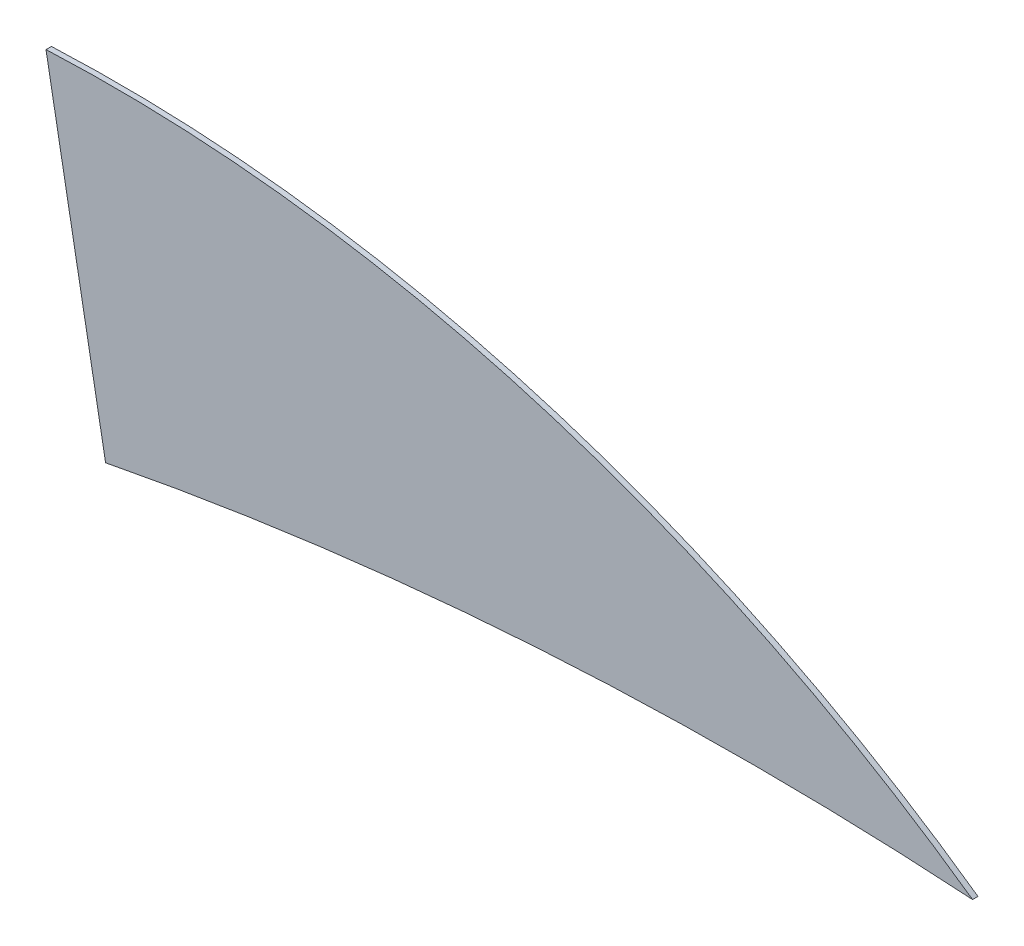
SolidWorks part; units mm, degrees
ref_plane "Alzado" through (0, 0, 0) normal (0, 0, 1) x (1, 0, 0)
ref_plane "Planta" through (0, 0, 0) normal (0, 1, 0) x (1, 0, 0)
ref_plane "Vista lateral" through (0, 0, 0) normal (1, 0, 0) x (0, 0, -1)
sketch "Model" plane through (0, 0, 0) normal (0, 0, 1) x (1, 0, 0)
  line L0 (21.4501, 16.559) -> (20.3504, 22.6137)
  arc A0 (37.4512, 17.5781) -> (20.3504, 22.6137) centre (21.5746, -4.7838) ccw
  arc A1 (37.4512, 17.5781) -> (21.4501, 16.559) centre (33.3826, -44.6625) ccw
extrude "Saliente-Extruir1" add sketch "Model" along normal blind 0.1
